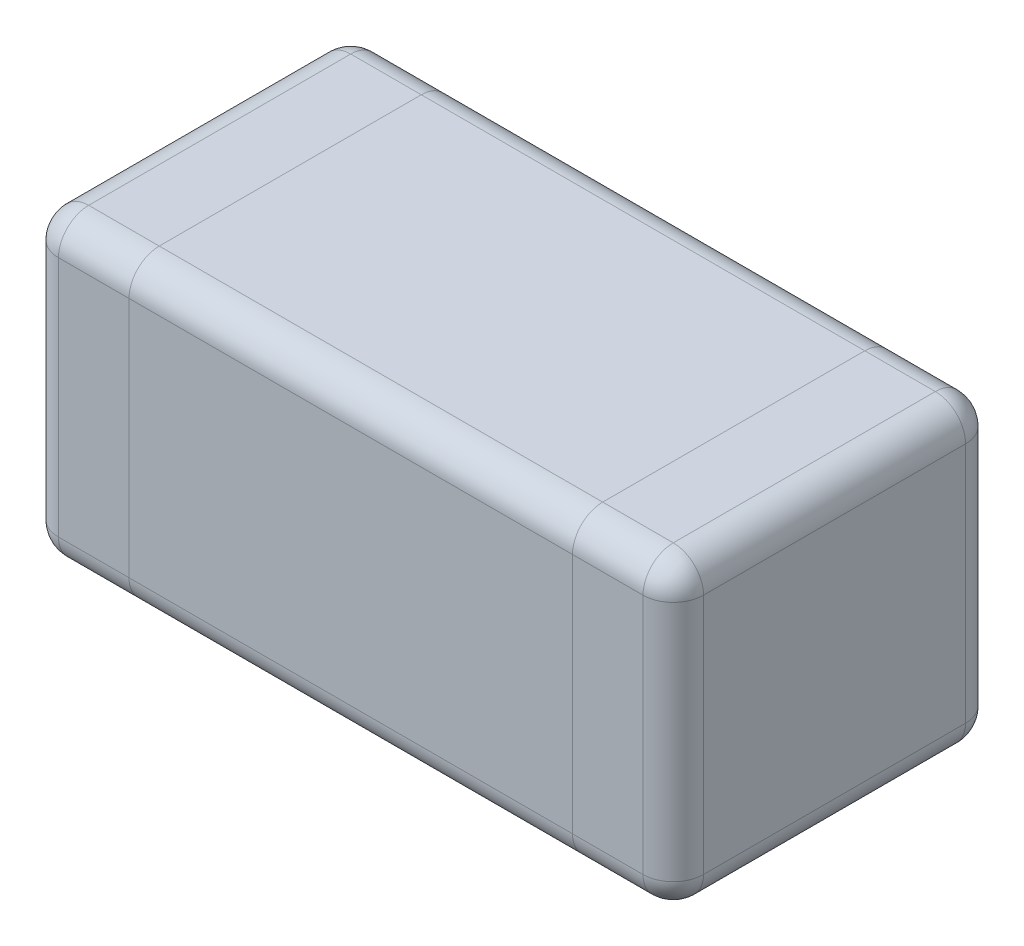
SolidWorks part; units mm, degrees
ref_plane "Front" through (0, 0, 0) normal (0, 0, 1) x (1, 0, 0)
ref_plane "Top" through (0, 0, 0) normal (0, 1, 0) x (1, 0, 0)
ref_plane "Right" through (0, 0, 0) normal (1, 0, 0) x (0, 0, -1)
sketch "Sketch1" plane through (0, 0, 0) normal (0, 1, 0) x (1, 0, 0)
  line L1 (1.1, -0.8) -> (-1.1, -0.8)
  line L2 (1.1, -0.8) -> (1.1, 0.8)
  line L3 (1.1, 0.8) -> (-1.1, 0.8)
  line L4 (-1.1, -0.8) -> (-1.1, 0.8)
  line L5 (1.1, -0.8) -> (-1.1, 0.8) construction
  line L6 (1.1, 0.8) -> (-1.1, -0.8) construction
  point P0 (0, 0)
  dimension "D1" = 1.6
  dimension "D2" = 2.2
extrude "Boss-Extrude1" add sketch "Sketch1" along normal blind 1.5
fillet "Fillet1" radius 0.15 4 edges at (0, 0, 0.8) (0, 1.5, 0.8) (0, 0, -0.8) (0, 1.5, -0.8)
sketch "Sketch2" plane through (1.1, 0, 0) normal (1, 0, 0) x (0, 0, -1)
  line L4 (-0.8, 1.35) -> (-0.8, 0.15)
  line L5 (-0.65, 0) -> (0.65, 0)
  line L6 (0.8, 0.15) -> (0.8, 1.35)
  line L7 (0.65, 1.5) -> (-0.65, 1.5)
  line L8 (-0.8, 1.35) -> (-0.8, 0.15)
  line L9 (-0.65, 0) -> (0.65, 0)
  line L10 (0.8, 0.15) -> (0.8, 1.35)
  line L11 (0.65, 1.5) -> (-0.65, 1.5)
  arc A4 (-0.8, 0.15) -> (-0.65, 0) centre (-0.65, 0.15) ccw
  arc A5 (0.65, 0) -> (0.8, 0.15) centre (0.65, 0.15) ccw
  arc A6 (0.8, 1.35) -> (0.65, 1.5) centre (0.65, 1.35) ccw
  arc A7 (-0.65, 1.5) -> (-0.8, 1.35) centre (-0.65, 1.35) ccw
  arc A8 (-0.8, 0.15) -> (-0.65, 0) centre (-0.65, 0.15) ccw
  arc A9 (0.65, 0) -> (0.8, 0.15) centre (0.65, 0.15) ccw
  arc A10 (0.8, 1.35) -> (0.65, 1.5) centre (0.65, 1.35) ccw
  arc A11 (-0.65, 1.5) -> (-0.8, 1.35) centre (-0.65, 1.35) ccw
  dimension "D1" = 0
extrude "Boss-Extrude2" add sketch "Sketch2" along normal blind 0.5 separate body
fillet "Fillet2" radius 0.15 8 edges at (1.6, 0.0439, -0.7561) (1.6, 0, 0) (1.6, 0.0439, 0.7561) (1.6, 0.75, 0.8) (1.6, 1.4561, 0.7561) (1.6, 1.5, 0) (1.6, 1.4561, -0.7561) (1.6, 0.75, -0.8)
mirror "Mirror1" about plane through (0, 0, 0) normal (1, 0, 0) of bodies 102
